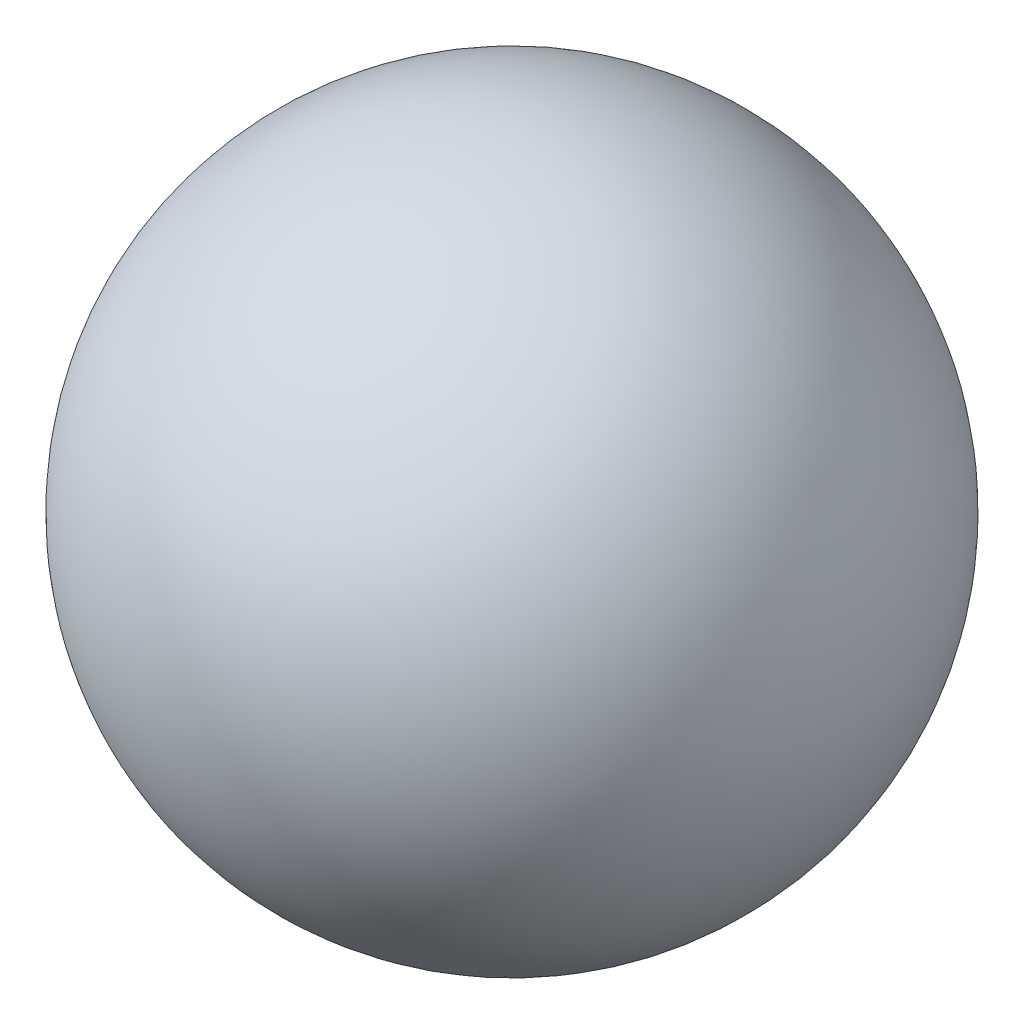
SolidWorks part; units mm, degrees
ref_plane "前视基准面" through (0, 0, 0) normal (0, 0, 1) x (1, 0, 0)
ref_plane "上视基准面" through (0, 0, 0) normal (0, 1, 0) x (1, 0, 0)
ref_plane "右视基准面" through (0, 0, 0) normal (1, 0, 0) x (0, 0, -1)
sketch "草图1" plane through (0, 0, 0) normal (0, 1, 0) x (1, 0, 0)
  line L0 (0, 6.9361) -> (0, -4.0328) construction
  circle A0 centre (0, 0) radius 3.5
  dimension "D1" = 7
revolve "旋转2" add sketch "草图1" angle 360 about L0
